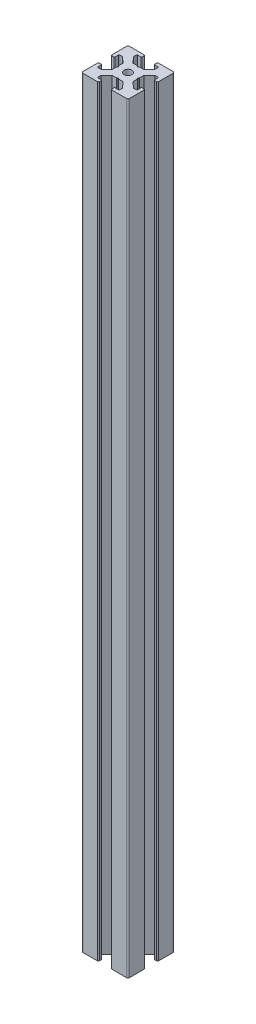
SolidWorks part; units mm, degrees
ref_plane "Front Plane" through (0, 0, 0) normal (0, 0, 1) x (1, 0, 0)
ref_plane "Top Plane" through (0, 0, 0) normal (0, 1, 0) x (1, 0, 0)
ref_plane "Right Plane" through (0, 0, 0) normal (1, 0, 0) x (0, 0, -1)
sketch "Sketch3" plane through (0, 0, 0) normal (0, 1, 0) x (1, 0, 0)
  line L0 (11, 30) -> (11, 27.75)
  line L1 (0, 0) -> (30, 0)
  line L2 (0, 0) -> (0, 30)
  line L3 (0, 30) -> (30, 30)
  line L4 (30, 0) -> (30, 30)
  line L5 (11, 27.75) -> (8, 27.75)
  line L6 (8, 27.75) -> (8, 25.5)
  line L7 (8, 25.5) -> (11.5, 21.75)
  line L8 (11.5, 21.75) -> (18.5, 21.75)
  line L9 (18.5, 21.75) -> (22, 25.5)
  line L10 (22, 25.5) -> (22, 27.75)
  line L11 (22, 27.75) -> (19, 27.75)
  line L12 (19, 27.75) -> (19, 30)
  line L13 (19, 30) -> (11, 30)
  line L14 (14.5, 21.75) -> (15, 21.25)
  line L15 (15, 21.25) -> (15.5, 21.75)
  line L16 (15.5, 21.75) -> (14.5, 21.75)
  line L17 (19, 29.5) -> (19, 30)
  line L18 (19.5, 30) -> (19, 30)
  line L19 (11, 29.5) -> (11, 30)
  line L20 (10.5, 30) -> (11, 30)
  line L21 (0, 19) -> (2.25, 19)
  line L22 (2.25, 19) -> (2.25, 22)
  line L23 (2.25, 22) -> (4.5, 22)
  line L24 (4.5, 22) -> (8.25, 18.5)
  line L25 (8.25, 18.5) -> (8.25, 11.5)
  line L26 (8.25, 11.5) -> (4.5, 8)
  line L27 (4.5, 8) -> (2.25, 8)
  line L28 (2.25, 8) -> (2.25, 11)
  line L29 (2.25, 11) -> (0, 11)
  line L30 (0, 11) -> (0, 19)
  line L31 (8.25, 15.5) -> (8.25, 14.5)
  line L32 (8.25, 14.5) -> (8.75, 15)
  line L33 (8.75, 15) -> (8.25, 15.5)
  line L34 (0.5, 19) -> (0, 19)
  line L35 (0, 19.5) -> (0, 19)
  line L36 (0, 10.5) -> (0, 11)
  line L37 (0.5, 11) -> (0, 11)
  line L38 (15, 30) -> (15, 0) construction
  line L39 (30, 15) -> (0, 15) construction
  line L40 (15, 8.75) -> (15.5, 8.25)
  line L41 (14.5, 8.25) -> (15, 8.75)
  line L42 (15.5, 8.25) -> (14.5, 8.25)
  line L43 (19.5, 0) -> (19, 0)
  line L44 (19, 0.5) -> (19, 0)
  line L45 (10.5, 0) -> (11, 0)
  line L46 (11, 0.5) -> (11, 0)
  line L47 (19, 2.25) -> (19, 0)
  line L48 (22, 2.25) -> (19, 2.25)
  line L49 (22, 4.5) -> (22, 2.25)
  line L50 (18.5, 8.25) -> (22, 4.5)
  line L51 (11.5, 8.25) -> (18.5, 8.25)
  line L52 (8, 4.5) -> (11.5, 8.25)
  line L53 (8, 2.25) -> (8, 4.5)
  line L54 (11, 2.25) -> (8, 2.25)
  line L55 (11, 0) -> (11, 2.25)
  line L56 (19, 0) -> (11, 0)
  line L57 (21.75, 14.5) -> (21.25, 15)
  line L58 (21.75, 15.5) -> (21.75, 14.5)
  line L59 (21.25, 15) -> (21.75, 15.5)
  line L60 (29.5, 11) -> (30, 11)
  line L61 (30, 10.5) -> (30, 11)
  line L62 (30, 19.5) -> (30, 19)
  line L63 (29.5, 19) -> (30, 19)
  line L64 (27.75, 11) -> (30, 11)
  line L65 (27.75, 8) -> (27.75, 11)
  line L66 (25.5, 8) -> (27.75, 8)
  line L67 (21.75, 11.5) -> (25.5, 8)
  line L68 (21.75, 18.5) -> (21.75, 11.5)
  line L69 (25.5, 22) -> (21.75, 18.5)
  line L70 (27.75, 22) -> (25.5, 22)
  line L71 (27.75, 19) -> (27.75, 22)
  line L72 (30, 19) -> (27.75, 19)
  line L73 (30, 11) -> (30, 19)
  arc A0 (19.5, 30) -> (19, 29.5) centre (19, 30) cw
  arc A1 (10.5, 30) -> (11, 29.5) centre (11, 30) ccw
  arc A2 (0.5, 19) -> (0, 19.5) centre (0, 19) ccw
  arc A3 (0.5, 11) -> (0, 10.5) centre (0, 11) cw
  arc A4 (19.5, 0) -> (19, 0.5) centre (19, 0) ccw
  arc A5 (10.5, 0) -> (11, 0.5) centre (11, 0) cw
  arc A6 (29.5, 11) -> (30, 10.5) centre (30, 11) ccw
  arc A7 (29.5, 19) -> (30, 19.5) centre (30, 19) cw
  point P7 (15, 21.75)
  point P16 (15, 30)
  point P26 (8.25, 15)
  point P35 (0, 15)
  dimension "D16" = 0.5
  dimension "D17" = 0.5
  dimension "D28" = 0.5
  dimension "D29" = 0.5
  dimension "D1" = 30
  dimension "D2" = 30
  dimension "D3" = 11
  dimension "D4" = 11
  dimension "D5" = 2.25
  dimension "D6" = 2.25
  dimension "D7" = 3
  dimension "D8" = 3
  dimension "D9" = 2.25
  dimension "D10" = 2.25
  dimension "D11" = 7
  dimension "D12" = 8.25
  dimension "D13" = 0.5
  dimension "D14" = 0.5
  dimension "D15" = 0.5
  dimension "D18" = 11
  dimension "D19" = 11
  dimension "D20" = 2.25
  dimension "D21" = 2.25
  dimension "D22" = 3
  dimension "D23" = 7
  dimension "D24" = 8.25
  dimension "D25" = 0.5
  dimension "D26" = 0.5
  dimension "D27" = 0.5
extrude "Boss-Extrude1" add sketch "Sketch3" along normal blind 490 contours L72 A7 L4 L3 A0 L12 L11 L10 L9 L8 L15 L14 L7 L6 L5 L0 A1 L2 A2 L21 L22 L23 L24 L25 L33 L32 L26 L27 L28 L29 A3 L1 A5 L55 L54 L53 L52 L51 L41 L40 L50 L49 L48 L47 A4
fillet "Fillet1" radius 1 4 edges at (0, 245, 0) (30, 245, 0) (30, 245, -30) (0, 245, -30)
sketch "Sketch4" plane through (0, 490, 0) normal (0, 1, 0) x (1, 0, 0)
  line L0 (18.5, 21.75) -> (8.25, 11.5) construction
  line L1 (21.75, 18.5) -> (11.5, 8.25) construction
  line L2 (15.5, 21.75) -> (21.75, 15.5) construction
  line L9 (8.25, 14.5) -> (14.5, 8.25) construction
  line L10 (8.25, 15.5) -> (14.5, 21.75) construction
  line L11 (21.75, 14.5) -> (15.5, 8.25) construction
  line L12 (11.5, 21.75) -> (21.75, 11.5) construction
  line L13 (8.25, 18.5) -> (18.5, 8.25) construction
  line L20 (30, 15) -> (0, 15) construction
  circle A0 centre (15, 15) radius 2.5
  dimension "D1" = 5
extrude "Cut-Extrude1" cut sketch "Sketch4" against normal through all
fillet "Fillet2" radius 0.5 24 edges at (2.25, 245, -22) (2.25, 245, -19) (8.25, 245, -15.5) (8.25, 245, -14.5) (2.25, 245, -11) (2.25, 245, -8) (8, 245, -2.25) (11, 245, -2.25) (14.5, 245, -8.25) (15.5, 245, -8.25) (19, 245, -2.25) (22, 245, -2.25) (27.75, 245, -8) (27.75, 245, -11) (27.75, 245, -19) (27.75, 245, -22) (21.75, 245, -14.5) (21.75, 245, -15.5) (15.5, 245, -21.75) (14.5, 245, -21.75) (22, 245, -27.75) (19, 245, -27.75) (11, 245, -27.75) (8, 245, -27.75)
